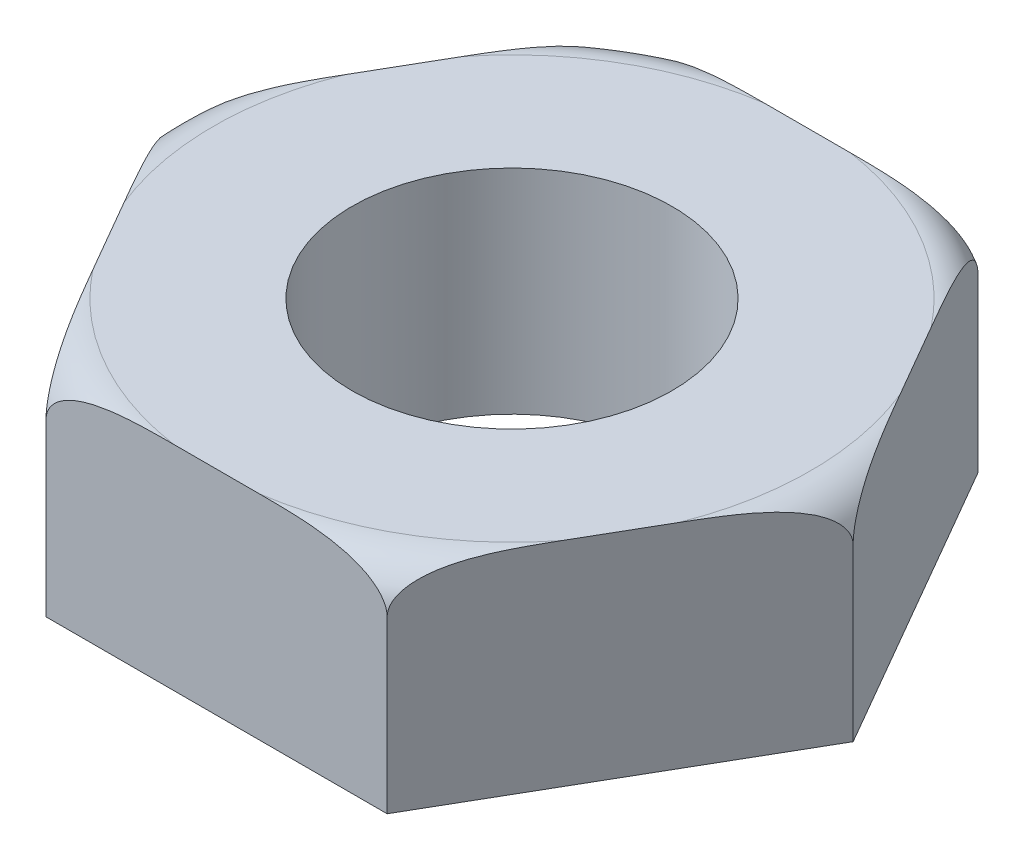
SolidWorks part; units mm, degrees
ref_plane "Front Plane" through (0, 0, 0) normal (0, 0, 1) x (1, 0, 0)
ref_plane "Top Plane" through (0, 0, 0) normal (0, 1, 0) x (1, 0, 0)
ref_plane "Right Plane" through (0, 0, 0) normal (1, 0, 0) x (0, 0, -1)
sketch "Sketch1" plane through (0, 0, 0) normal (0, 1, 0) x (1, 0, 0)
  line L1 (40, 0) -> (20, 34.641)
  line L2 (20, 34.641) -> (-20, 34.641)
  line L3 (-20, 34.641) -> (-40, 0)
  line L4 (-40, 0) -> (-20, -34.641)
  line L5 (-20, -34.641) -> (20, -34.641)
  line L6 (20, -34.641) -> (40, 0)
  dimension "D1" = 80
extrude "Boss-Extrude1" add sketch "Sketch1" along normal blind 25
sketch "Sketch2" plane through (0, 0, 0) normal (0, 0, 1) x (1, 0, 0)
  line L0 (-40, 19.7877) -> (-40, 20)
  line L3 (-20, 25) -> (20, 25) construction
  line L4 (-40, 25) -> (-40, 0) construction
  line L6 (-40, 25) -> (-20, 25) construction
  line L7 (0, 25) -> (0, 47.2601) construction
  line L8 (-35, 25) -> (-37.7577, 31.268)
  line L9 (-37.7577, 31.268) -> (-44.9727, 23.7639)
  line L10 (-44.9727, 23.7639) -> (-40, 19.7877)
  arc A0 (-40, 20) -> (-35, 25) centre (-35, 20) cw
  point P15 (-40, 25)
  dimension "D1" = 5
revolve "Cut-Revolve1" cut sketch "Sketch2" angle 360 about L7
sketch "Sketch3" plane through (0, 25, 0) normal (0, 1, 0) x (1, 0, 0)
  circle A0 centre (0, 0) radius 18.75
  dimension "D1" = 37.5
extrude "Cut-Extrude1" cut sketch "Sketch3" against normal blind 49
